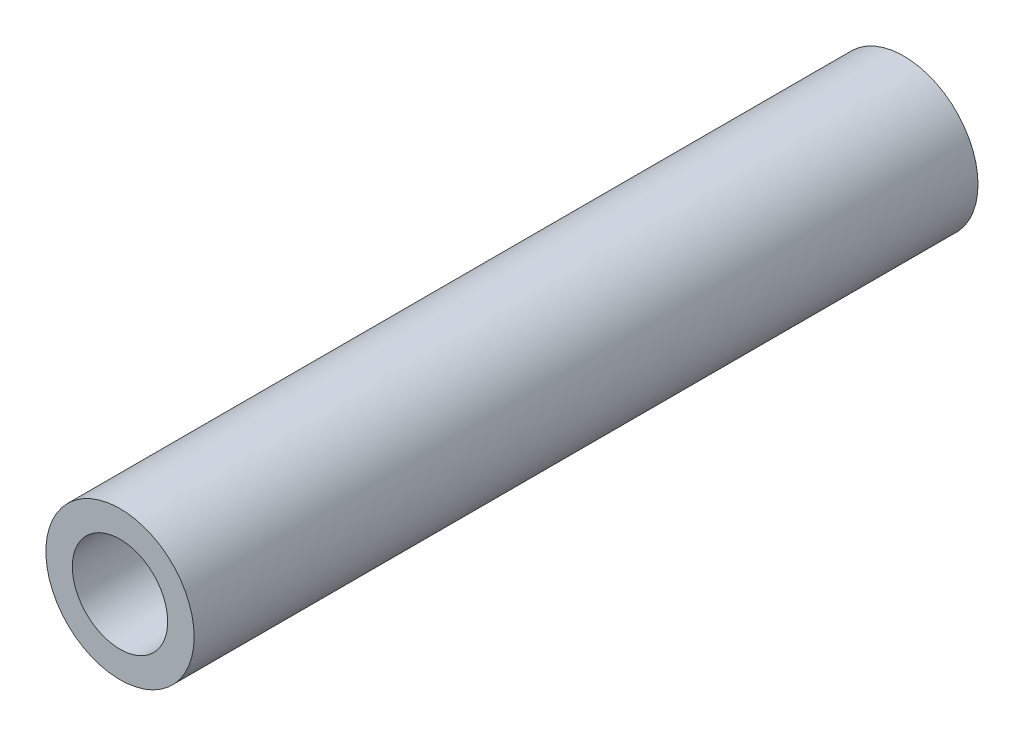
SolidWorks part; units mm, degrees
ref_plane "Front Plane" through (0, 0, 0) normal (0, 0, 1) x (1, 0, 0)
ref_plane "Top Plane" through (0, 0, 0) normal (0, 1, 0) x (1, 0, 0)
ref_plane "Right Plane" through (0, 0, 0) normal (1, 0, 0) x (0, 0, -1)
sketch "Sketch1" plane through (0, 0, 0) normal (0, 0, 1) x (1, 0, 0)
  circle A0 centre (0, 0) radius 3.5
  dimension "D1" = 7
extrude "Boss-Extrude1" add sketch "Sketch1" along normal blind 37 contours A0
hole_wizard "M4 Clearance Hole1" positions "Sketch4" profile "Sketch3" hole size "M4" standard "ANSI Metric" end condition through all
sketch "Sketch4" plane through (0, 0, 0) normal (0, 0, -1) x (-1, 0, 0)
  point P0 (0, 0)
sketch "Sketch3" plane through (0, 0, 0) normal (1, 0, 0) x (0, 1, 0)
  line L0 (0, 0) -> (0, 37)
  line L1 (0, 37) -> (2.25, 37)
  line L2 (2.25, 37) -> (2.25, 0)
  line L5 (2.25, 0) -> (0, 0)
  line L11 (0, -6.35) -> (0, 107.95) construction
  dimension "Thru Hole Dia." = 4.5
  dimension "Thru Hole Depth" = 37
